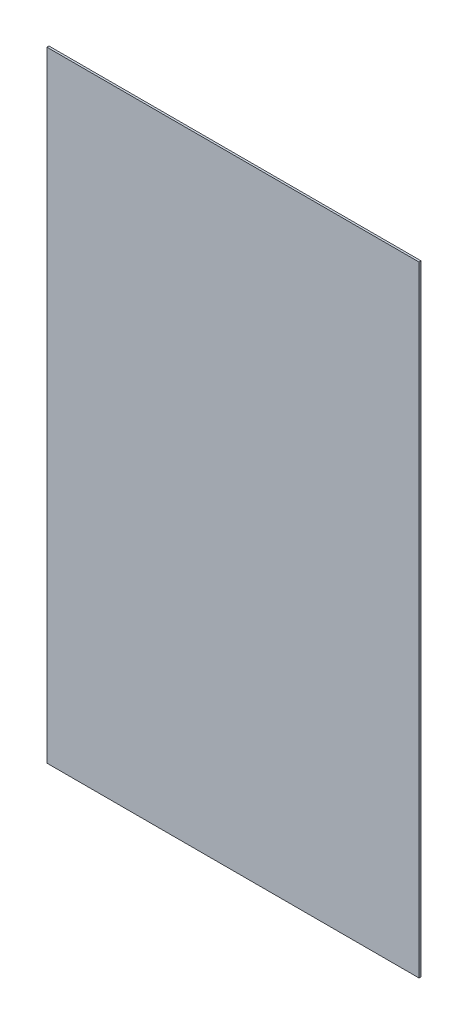
SolidWorks part; units mm, degrees
ref_plane "前视基准面" through (0, 0, 0) normal (0, 0, 1) x (1, 0, 0)
ref_plane "上视基准面" through (0, 0, 0) normal (0, 1, 0) x (1, 0, 0)
ref_plane "右视基准面" through (0, 0, 0) normal (1, 0, 0) x (0, 0, -1)
sketch "草图1" plane through (0, 0, 0) normal (0, 0, 1) x (1, 0, 0)
  line L1 (-9, -15) -> (9, -15)
  line L2 (-9, -15) -> (-9, 15)
  line L3 (-9, 15) -> (9, 15)
  line L4 (9, -15) -> (9, 15)
  line L5 (-9, -15) -> (9, 15) construction
  line L6 (-9, 15) -> (9, -15) construction
  point P0 (0, 0)
  dimension "D1" = 18
  dimension "D2" = 30
extrude "凸台-拉伸1" add sketch "草图1" along normal blind 0.1 contours L2 L3 L4 L1
